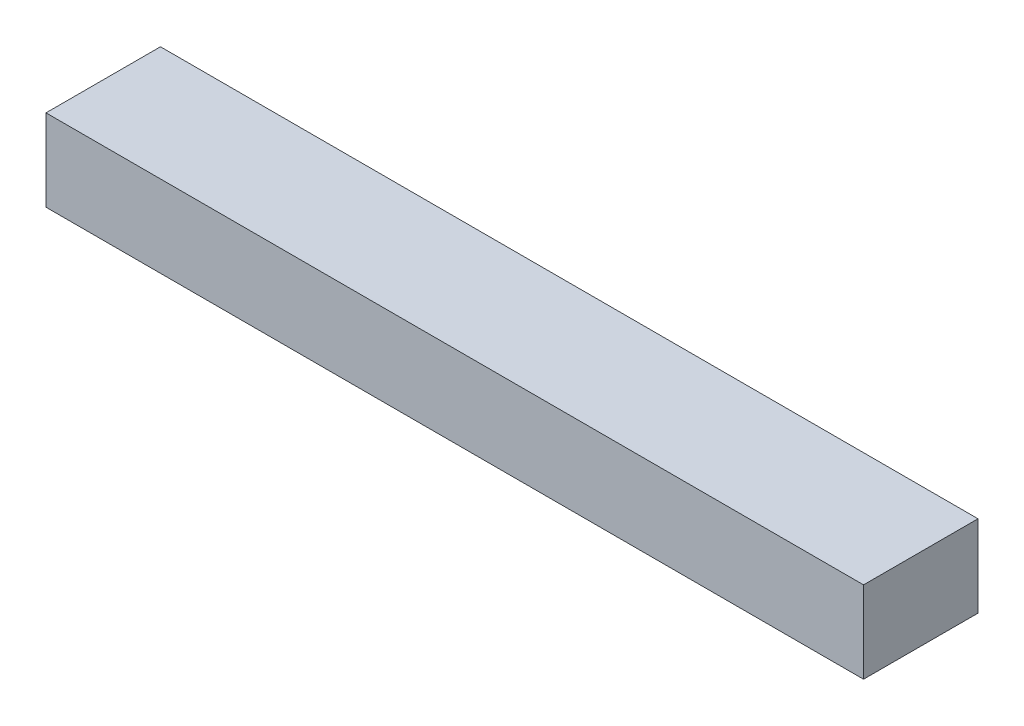
SolidWorks part; units mm, degrees
ref_plane "Front Plane" through (0, 0, 0) normal (0, 0, 1) x (1, 0, 0)
ref_plane "Top Plane" through (0, 0, 0) normal (0, 1, 0) x (1, 0, 0)
ref_plane "Right Plane" through (0, 0, 0) normal (1, 0, 0) x (0, 0, -1)
sketch "Sketch1" plane through (0, 0, 0) normal (0, 0, 1) x (1, 0, 0)
  line L1 (-5, 0.5) -> (5, 0.5)
  line L2 (-5, 0.5) -> (-5, -0.5)
  line L3 (-5, -0.5) -> (5, -0.5)
  line L4 (5, 0.5) -> (5, -0.5)
  line L5 (-5, 0.5) -> (5, -0.5) construction
  line L6 (-5, -0.5) -> (5, 0.5) construction
  point P0 (0, 0)
  dimension "D1" = 10
  dimension "D2" = 1
extrude "Boss-Extrude1" add sketch "Sketch1" along normal blind 2
other "Move Face1" face at (0, 0, 0) parameters "D1"=0.3
other "Move Face2" face at (0, 0, 2) parameters "D1"=0.3
